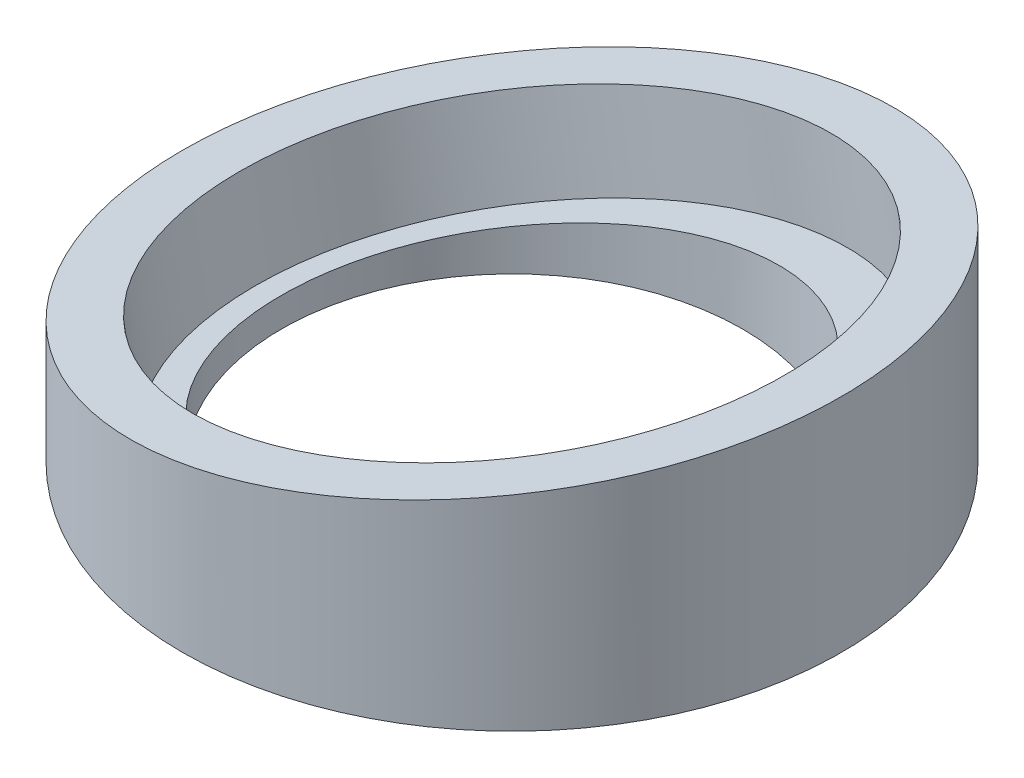
SolidWorks part; units mm, degrees
ref_plane "前视基准面" through (0, 0, 0) normal (0, 0, 1) x (1, 0, 0)
ref_plane "上视基准面" through (0, 0, 0) normal (0, 1, 0) x (1, 0, 0)
ref_plane "右视基准面" through (0, 0, 0) normal (1, 0, 0) x (0, 0, -1)
sketch "草图1" plane through (0, 0, 0) normal (0, 1, 0) x (1, 0, 0)
  circle A0 centre (0, 0) radius 25
  dimension "D1" = 50
extrude "凸台-拉伸1" add sketch "草图1" along normal blind 20
sketch "草图2" plane through (0, 20, 0) normal (0, 1, 0) x (1, 0, 0)
  circle A0 centre (0, 0) radius 17.5
  dimension "D1" = 35
extrude "切除-拉伸1" cut sketch "草图2" against normal blind 20
sketch "草图3" plane through (0, 0, 0) normal (0, 0, 1) x (1, 0, 0)
  line L0 (-25, 8) -> (27.3953, 17.2387)
  line L1 (-25, 20) -> (-25, 0) construction
  line L2 (27.3953, 17.2387) -> (27.2584, 39.9343)
  line L3 (27.2584, 39.9343) -> (-34.8284, 34.2564)
  line L4 (-34.8284, 34.2564) -> (-25, 8)
  line L5 (-25, 0) -> (25, 0) construction
  dimension "D1" = 8
  dimension "D2" = 10
extrude "切除-拉伸2" cut sketch "草图3" against normal mid plane 77
sketch "草图4" plane through (-2.1219, 12.034, 0) normal (-0.1736, 0.9848, 0) x (0.9848, 0.1736, 0)
  circle A0 centre (2.1547, 0) radius 21
  dimension "D1" = 42
extrude "切除-拉伸3" cut sketch "草图4" against normal blind 7
